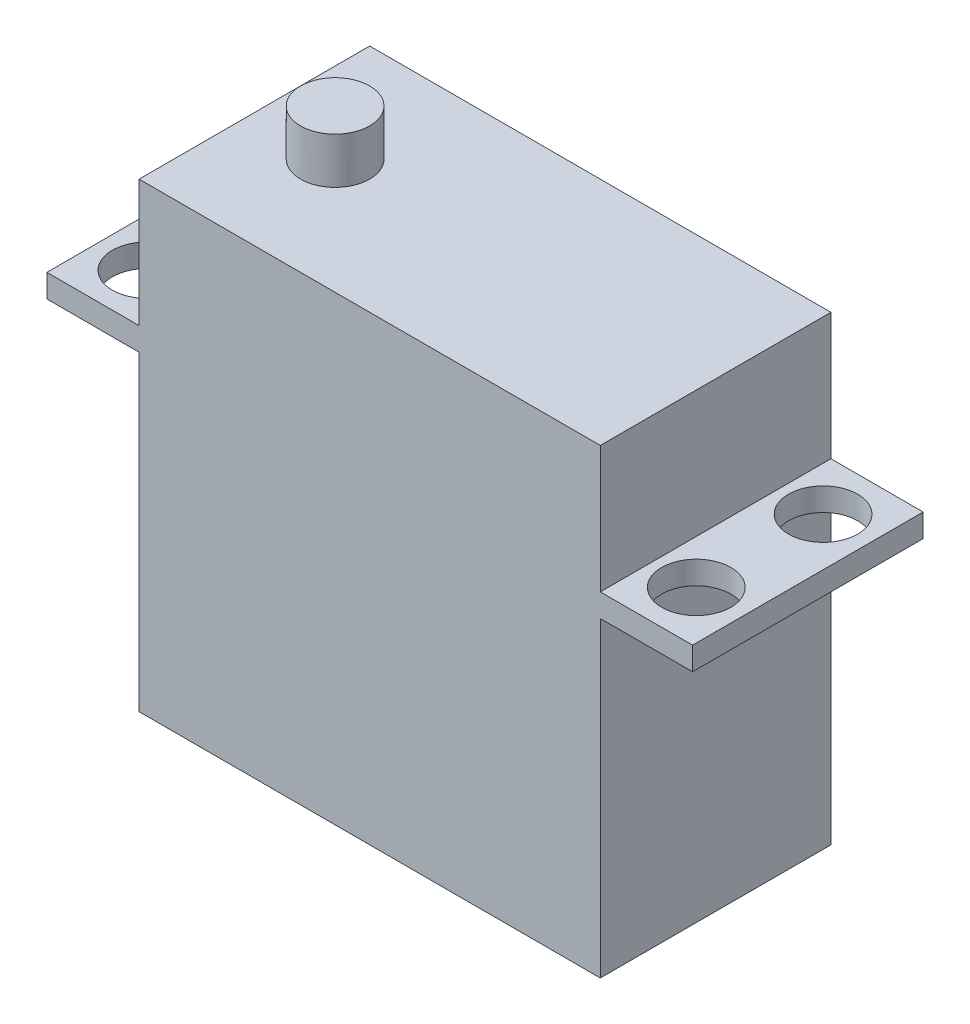
SolidWorks part; units mm, degrees
ref_plane "Front Plane" through (0, 0, 0) normal (0, 0, 1) x (1, 0, 0)
ref_plane "Top Plane" through (0, 0, 0) normal (0, 1, 0) x (1, 0, 0)
ref_plane "Right Plane" through (0, 0, 0) normal (1, 0, 0) x (0, 0, -1)
sketch "Sketch1" plane through (0, 0, 0) normal (0, 1, 0) x (1, 0, 0)
  line L1 (-20, -10) -> (20, -10)
  line L2 (-20, -10) -> (-20, 10)
  line L3 (-20, 10) -> (20, 10)
  line L4 (20, -10) -> (20, 10)
  line L5 (-20, -10) -> (20, 10) construction
  line L6 (-20, 10) -> (20, -10) construction
  point P0 (0, 0)
  dimension "D1" = 20
  dimension "D2" = 40
extrude "Boss-Extrude1" add sketch "Sketch1" along normal blind 40
sketch "Sketch2" plane through (0, 40, 0) normal (0, 1, 0) x (1, 0, 0)
  line L0 (-20, 10) -> (-20, -10) construction
  circle A0 centre (-13, 0) radius 3
  dimension "D1" = 7
  dimension "D2" = 6
extrude "Boss-Extrude2" add sketch "Sketch2" along normal blind 4
sketch "Sketch3" plane through (20, 0, 0) normal (1, 0, 0) x (0, 0, -1)
  line L0 (-10, 40) -> (-10, 0) construction
  line L1 (-10, 29) -> (10, 29)
  line L2 (-10, 29) -> (-10, 27)
  line L3 (-10, 27) -> (10, 27)
  line L4 (10, 29) -> (10, 27)
  line L5 (10, 40) -> (10, 0) construction
  line L6 (-10, 0) -> (10, 0) construction
  dimension "D1" = 2
  dimension "D2" = 27
extrude "Boss-Extrude3" add sketch "Sketch3" along normal blind 8
sketch "Sketch4" plane through (0, 29, 0) normal (0, 1, 0) x (1, 0, 0)
  line L0 (28, 10) -> (20, 10) construction
  circle A0 centre (23.8219, 5.5) radius 3
  circle A1 centre (23.8219, -5.5) radius 3
  dimension "D1" = 6
  dimension "D2" = 6
  dimension "D4" = 11
  dimension "D3" = 4.5
extrude "Cut-Extrude1" cut sketch "Sketch4" against normal through all
mirror "Mirror2" about plane through (0, 0, 0) normal (1, 0, 0) of "Cut-Extrude1", "Boss-Extrude3"
